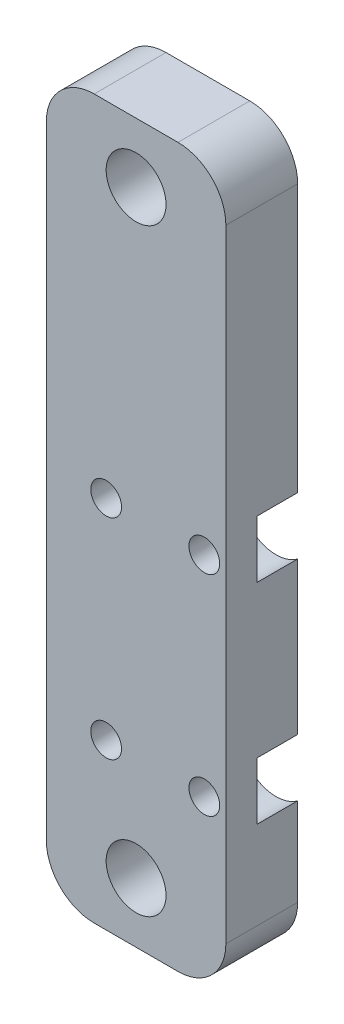
SolidWorks part; units mm, degrees
ref_plane "Front Plane" through (0, 0, 0) normal (0, 0, 1) x (1, 0, 0)
ref_plane "Top Plane" through (0, 0, 0) normal (0, 1, 0) x (1, 0, 0)
ref_plane "Right Plane" through (0, 0, 0) normal (1, 0, 0) x (0, 0, -1)
sketch "Sketch1" plane through (0, 0, 0) normal (0, 0, 1) x (1, 0, 0)
  line L1 (-13.97, 28.575) -> (5.08, 28.575)
  line L2 (-13.97, 28.575) -> (-13.97, -47.625)
  line L3 (-13.97, -47.625) -> (5.08, -47.625)
  line L4 (5.08, 28.575) -> (5.08, -47.625)
  dimension "D1" = 76.2
  dimension "D2" = 19.05
  dimension "D3" = 13.97
  dimension "D4" = 28.575
extrude "Boss-Extrude1" add sketch "Sketch1" along normal blind 7.62
hole_wizard "1/4 (0.25) Diameter Hole1" positions "Sketch3" profile "Sketch2" hole size "1/4" standard "ANSI Inch"
sketch "Sketch3" plane through (0, 0, 7.62) normal (0, 0, 1) x (1, 0, 0)
  line L1 (5.08, -47.625) -> (5.08, 28.575) construction
  line L2 (5.08, 28.575) -> (-13.97, 28.575) construction
  point P0 (-4.445, 22.225)
  point P2 (-4.445, -41.275)
  point P14 (-4.445, 28.575)
  dimension "D1" = 6.35
  dimension "D2" = 63.5
  dimension "D3" = 9.525
  dimension "D4" = 9.525
sketch "Sketch2" plane through (-4.445, 22.225, 7.62) normal (1, 0, 0) x (0, -1, 0)
  line L0 (0, 0) -> (0, 27.3077)
  line L1 (0, 27.3077) -> (3.175, 25.4)
  line L2 (3.175, 25.4) -> (3.175, 0)
  line L5 (3.175, 0) -> (0, 0)
  line L10 (0, 27.3077) -> (-3.175, 25.4) construction
  line L11 (0, -6.35) -> (0, 107.95) construction
  dimension "Hole Dia." = 6.35
  dimension "Hole Depth" = 25.4
  dimension "Drill Angle" = 118
hole_wizard "CBORE for #4 Socket Head Cap Screw5" positions "Sketch6" profile "Sketch5" counterbore size "#4" standard "ANSI Inch" end condition through all
sketch "Sketch6" plane through (-2.0173, -3.8136, 0) normal (0, 0, 1) x (1, 0, 0)
  line L1 (-11.9527, 32.3886) -> (-11.9527, -43.8114) construction
  circle A1 centre (-2.4277, -37.4614) radius 3.175 construction
  point P0 (-5.6027, -4.1239)
  point P2 (-5.6027, -26.3489)
  point P4 (4.8113, -26.3489)
  point P6 (4.8113, -4.1239)
  dimension "D1" = 22.225
  dimension "D2" = 10.414
  dimension "D3" = 11.1125
  dimension "D4" = 6.35
sketch "Sketch5" plane through (-7.62, -7.9375, 0) normal (1, 0, 0) x (0, 1, 0)
  line L0 (0, 0) -> (0, 7.62)
  line L1 (0, 7.62) -> (1.632, 7.62)
  line L3 (1.632, 7.62) -> (1.6319, 4.318)
  line L4 (1.6319, 4.318) -> (3.81, 4.318)
  line L5 (3.81, 4.318) -> (3.81, 0)
  line L7 (3.81, 0) -> (0, 0)
  line L11 (0, -6.35) -> (0, 107.95) construction
  dimension "Thru Hole Dia." = 3.2639
  dimension "Thru Hole Depth" = 7.62
  dimension "C'Bore Dia." = 7.62
  dimension "C'Bore Depth" = 4.318
fillet "Fillet1" radius 5.08 4 edges at (5.08, 28.575, 3.81) (5.08, -47.625, 3.81) (-13.97, -47.625, 3.81) (-13.97, 28.575, 3.81)
sketch "Sketch7" plane through (0, 28.575, 0) normal (0, 1, 0) x (1, 0, 0)
  line L0 (-4.445, -7.62) -> (-4.445, 4.38)
  line L1 (0, -7.62) -> (-8.89, -7.62) construction
  line L2 (0, 0) -> (-8.89, 0) construction
  dimension "D1" = 12
  dimension "D2" = 4.38
